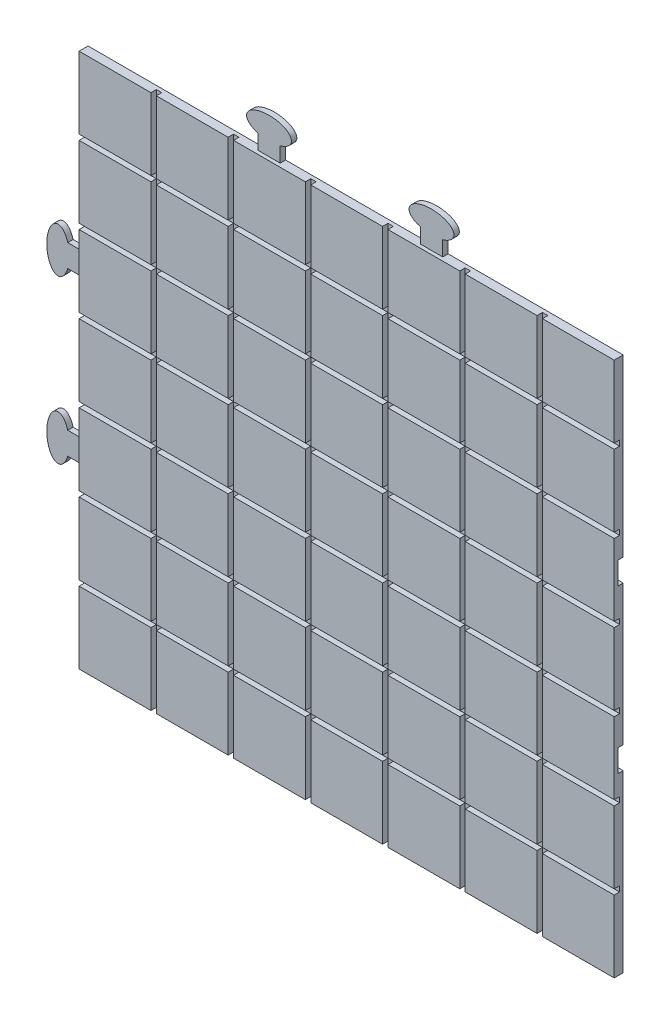
SolidWorks part; units mm, degrees
ref_plane "Plan de face" through (0, 0, 0) normal (0, 0, 1) x (1, 0, 0)
ref_plane "Plan de dessus" through (0, 0, 0) normal (0, 1, 0) x (1, 0, 0)
ref_plane "Plan de droite" through (0, 0, 0) normal (1, 0, 0) x (0, 0, -1)
sketch "Esquisse1" plane through (0, 0, 0) normal (0, 0, 1) x (1, 0, 0)
  line L1 (-149, -149) -> (149, -149)
  line L2 (-149, -149) -> (-149, 149)
  line L3 (-149, 149) -> (149, 149)
  line L4 (149, -149) -> (149, 149)
  line L5 (-149, -149) -> (149, 149) construction
  line L6 (-149, 149) -> (149, -149) construction
  point P0 (0, 0)
  dimension "D1" = 298
  dimension "D2" = 298
extrude "Boss.-Extru.1" add sketch "Esquisse1" along normal blind 5
sketch "Esquisse2" plane through (0, 0, 5) normal (0, 0, 1) x (1, 0, 0)
  line L0 (149, 149) -> (-149, 149) construction
  line L1 (-109, 149) -> (-106, 149)
  line L2 (-109, 149) -> (-109, -149)
  line L3 (-109, -149) -> (-106, -149)
  line L4 (-106, 149) -> (-106, -149)
  line L5 (-149, -149) -> (149, -149) construction
  line L6 (149, -149) -> (149, 149) construction
  line L7 (-66, 149) -> (-63, 149)
  line L8 (-66, 149) -> (-66, -149)
  line L9 (-66, -149) -> (-63, -149)
  line L10 (-63, 149) -> (-63, -149)
  line L11 (-23, 149) -> (-20, 149)
  line L12 (-23, 149) -> (-23, -149)
  line L13 (-23, -149) -> (-20, -149)
  line L14 (-20, 149) -> (-20, -149)
  line L15 (20, 149) -> (23, 149)
  line L16 (20, 149) -> (20, -149)
  line L17 (20, -149) -> (23, -149)
  line L18 (23, 149) -> (23, -149)
  line L19 (63, 149) -> (66, 149)
  line L20 (63, 149) -> (63, -149)
  line L21 (63, -149) -> (66, -149)
  line L22 (66, 149) -> (66, -149)
  line L23 (106, 149) -> (109, 149)
  line L24 (106, 149) -> (106, -149)
  line L25 (106, -149) -> (109, -149)
  line L26 (109, 149) -> (109, -149)
  line L28 (-149, 66) -> (149, 66)
  line L29 (-149, 66) -> (-149, 63)
  line L30 (-149, 63) -> (149, 63)
  line L31 (149, 66) -> (149, 63)
  line L32 (149, 23) -> (-149, 23)
  line L33 (149, 23) -> (149, 20)
  line L34 (149, 20) -> (-149, 20)
  line L35 (-149, 23) -> (-149, 20)
  line L36 (-149, -20) -> (149, -20)
  line L37 (-149, -20) -> (-149, -23)
  line L38 (-149, -23) -> (149, -23)
  line L39 (149, -20) -> (149, -23)
  line L40 (-149, -63) -> (149, -63)
  line L41 (-149, -63) -> (-149, -66)
  line L42 (-149, -66) -> (149, -66)
  line L43 (149, -63) -> (149, -66)
  line L44 (-149, -106) -> (149, -106)
  line L45 (-149, -106) -> (-149, -109)
  line L46 (-149, -109) -> (149, -109)
  line L47 (149, -106) -> (149, -109)
  line L56 (149, 109) -> (-149, 109)
  line L58 (149, 109) -> (149, 106)
  line L60 (149, 106) -> (-149, 106)
  line L62 (-149, 109) -> (-149, 106)
  line L63 (-149, 149) -> (-149, -149) construction
  dimension "D1" = 40
  dimension "D2" = 3
  dimension "D3" = 40
  dimension "D4" = 3
  dimension "D5" = 40
  dimension "D6" = 3
  dimension "D7" = 40
  dimension "D8" = 3
  dimension "D9" = 40
  dimension "D10" = 3
  dimension "D11" = 40
  dimension "D12" = 3
  dimension "D13" = 40
  dimension "D14" = 40
  dimension "D15" = 3
  dimension "D17" = 40
  dimension "D18" = 40
  dimension "D16" = 3
  dimension "D19" = 3
  dimension "D20" = 40
  dimension "D21" = 3
  dimension "D22" = 3
  dimension "D23" = 40
  dimension "D24" = 3
  dimension "D25" = 40
  dimension "D26" = 40
extrude "Enlèv. mat.-Extru.5" cut sketch "Esquisse2" against normal blind 3 contours L2 L3 L4 L1 | L10 L9 L8 L7 | L12 L13 L14 L11 | L56 L62 L60 L58 | L28 L31 L30 L29 | L32 L35 L34 L33 | L36 L39 L38 L37 | L40 L43 L42 L41 | L44 L47 L46 L45 | L16 L17 L18 L15 | L20 L21 L22 L19 | L24 L25 L26 L23
sketch "Esquisse3" plane through (0, 0, 0) normal (0, 0, -1) x (-1, 0, 0)
  line L0 (-51.5, -135.25) -> (-39, -135.25)
  line L1 (-51.5, -135.25) -> (-51.5, -149)
  line L2 (-39, -135.25) -> (-39, -149)
  line L3 (-51.5, -149) -> (-39, -149)
  line L4 (149, -149) -> (-149, -149) construction
  line L5 (-149, -149) -> (-149, 149) construction
  line L6 (-149, 149) -> (149, -149) construction
  line L7 (149, 149) -> (-149, -149) construction
  line L8 (0, 0) -> (0, 155.605) construction
  line L9 (51.5, -149) -> (39, -149)
  line L10 (39, -135.25) -> (39, -149)
  line L11 (51.5, -135.25) -> (51.5, -149)
  line L12 (51.5, -135.25) -> (39, -135.25)
  line L13 (-149, -51.5) -> (-149, -39)
  line L14 (-135.25, -51.5) -> (-149, -51.5)
  line L15 (-135.25, -39) -> (-149, -39)
  line L16 (-135.25, -51.5) -> (-135.25, -39)
  line L17 (-149, 51.5) -> (-149, 39)
  line L18 (-135.25, 51.5) -> (-149, 51.5)
  line L19 (-135.25, 51.5) -> (-135.25, 39)
  line L20 (-135.25, 39) -> (-149, 39)
  ellipse E0 centre (-45.25, -135.25) end of major axis (-57.75, -135.25) minor radius 6.25
  ellipse E1 centre (45.25, -135.25) end of major axis (57.75, -135.25) minor radius 6.25
  ellipse E2 centre (-135.25, -45.25) end of major axis (-135.25, -57.75) minor radius 6.25
  ellipse E3 centre (-135.25, 45.25) end of major axis (-135.25, 57.75) minor radius 6.25
  point P1 (-45.25, -149)
  point P58 (0, 0)
  line M3 (-149, 149) -> (-149, -149)
  line M4 (-149, -149) -> (149, -149)
  dimension "D1" = 6.25
  dimension "D2" = 6.25
  dimension "D3" = 20
  dimension "D4" = 25
  dimension "D5" = 12.5
  dimension "D6" = 97.5
  dimension "D7" = 2
sketch "Esquisse4" plane through (0, 0, 0) normal (0, 0, -1) x (-1, 0, 0)
  line L0 (149, 39) -> (162.75, 39)
  line L1 (-149, -149) -> (-149, 149) construction
  line L2 (0, 0) -> (0, 210.2285) construction
  line L3 (51.5, 149) -> (39, 149)
  line L4 (51.5, 162.75) -> (51.5, 149)
  line L5 (39, 149) -> (39, 162.75)
  line L6 (39, 162.75) -> (51.5, 162.75)
  line L7 (162.75, 39) -> (162.75, 51.5)
  line L8 (-39, 162.75) -> (-51.5, 162.75)
  line L9 (-39, 149) -> (-39, 162.75)
  line L10 (-51.5, 149) -> (-39, 149)
  line L11 (-51.5, 162.75) -> (-51.5, 149)
  line L12 (162.75, 51.5) -> (149, 51.5)
  line L13 (149, 51.5) -> (149, 39)
  line L14 (149, -51.5) -> (149, -39)
  line L15 (162.75, -51.5) -> (149, -51.5)
  line L16 (149, -39) -> (162.75, -39)
  line L17 (162.75, -39) -> (162.75, -51.5)
  ellipse E0 centre (45.25, 162.75) end of major axis (57.75, 162.75) minor radius 6.25
  ellipse E1 centre (162.75, 45.25) end of major axis (162.75, 57.75) minor radius 6.25
  ellipse E2 centre (-45.25, 162.75) end of major axis (-57.75, 162.75) minor radius 6.25
  ellipse E3 centre (162.75, -45.25) end of major axis (162.75, -57.75) minor radius 6.25
  point P48 (0, 0)
  line M18 (149, -149) -> (149, 149)
  line M19 (149, 149) -> (-149, 149)
  dimension "D1" = 97.5
  dimension "D2" = 103.75
  dimension "D3" = 2
extrude "Boss.-Extru.2" add sketch "Esquisse4" against normal blind 3 contours L11 E2 L9 L8 | E2 L11 L9 M19 | L9 E2 L11 L8 | L4 E0 L5 M19 | E0 L4 L6 L5 | E0 L5 L6 L4 | L15 E3 L16 M18 | E3 L15 L17 L16 | E3 L16 L17 L15 | E1 L12 L0 M18 | L12 E1 L0 L7 | L0 E1 L12 L7
extrude "Enlèv. mat.-Extru.6" cut sketch "Esquisse3" against normal blind 3 contours L11 E1 L10 M4 | E1 L11 L12 L10 | E1 L10 L12 L11 | E0 L1 L2 M4 | L1 E0 L2 L0 | L2 E0 L1 L0 | L14 E2 L15 M3 | E2 L14 L16 L15 | E2 L15 L16 L14 | E3 L18 L20 M3 | L18 E3 L20 L19 | L20 E3 L18 L19
